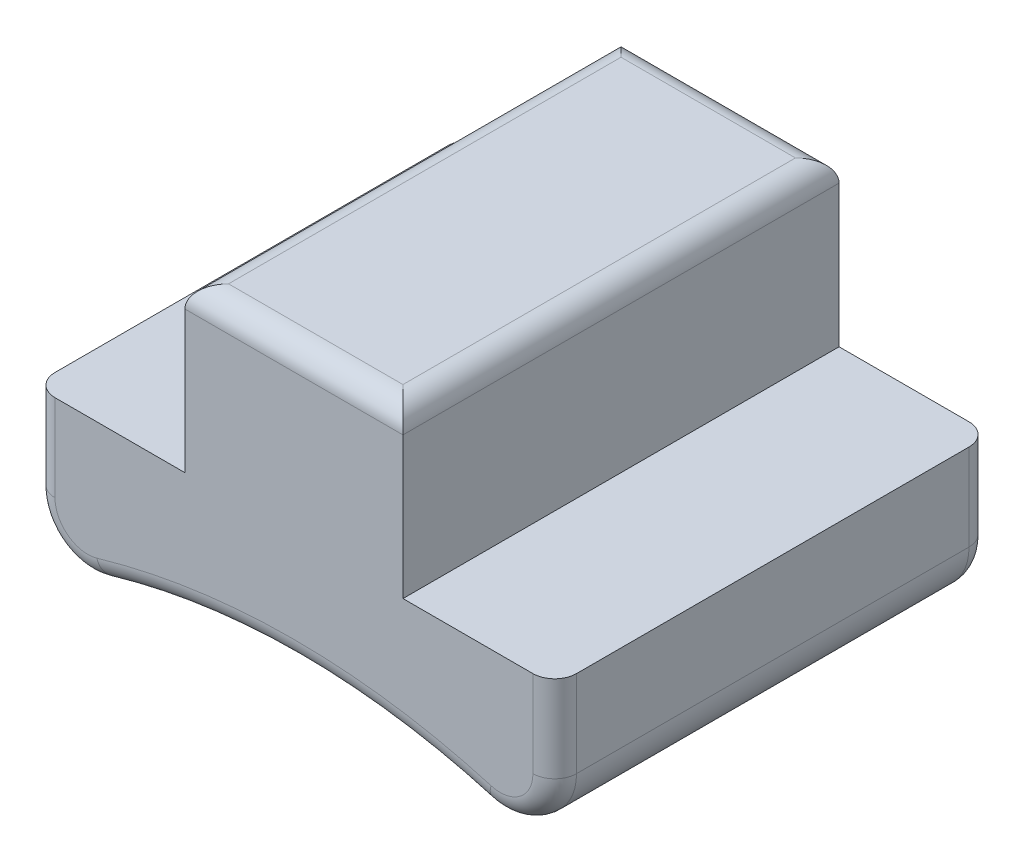
SolidWorks part; units mm, degrees
ref_plane "Front Plane" through (0, 0, 0) normal (0, 0, 1) x (1, 0, 0)
ref_plane "Top Plane" through (0, 0, 0) normal (0, 1, 0) x (1, 0, 0)
ref_plane "Right Plane" through (0, 0, 0) normal (1, 0, 0) x (0, 0, -1)
sketch "Sketch1" plane through (0, 0, 0) normal (0, 0, 1) x (1, 0, 0)
  line L0 (0, 0) -> (0, 120.9016) construction
  line L1 (-12.7, 111.4329) -> (12.7, 111.4329)
  line L2 (12.7, 111.4329) -> (12.7, 92.3829)
  line L3 (12.7, 92.3829) -> (30.3755, 92.3829)
  line L4 (30.3755, 92.3829) -> (30.3755, 73.3329)
  line L5 (-12.7, 111.4329) -> (-12.7, 92.3829)
  line L6 (-12.7, 92.3829) -> (-30.3755, 92.3829)
  line L7 (-30.3755, 92.3829) -> (-30.3755, 73.3329)
  line L8 (-30.3755, 73.3329) -> (0, 0) construction
  line L9 (0, 0) -> (30.3755, 73.3329) construction
  arc A0 (30.3755, 73.3329) -> (-30.3755, 73.3329) centre (0, 0) ccw
  point P10 (0, 111.4329)
  dimension "D1" = 158.75
  dimension "D2" = 45
  dimension "D3" = 25.4
  dimension "D4" = 19.05
  dimension "D5" = 19.05
extrude "Boss-Extrude1" add sketch "Sketch1" along normal blind 50.8
fillet "Fillet1" radius 6.35 2 edges at (-30.3755, 73.3329, 25.4) (30.3755, 73.3329, 25.4)
fillet "Fillet3" radius 2.54 4 edges at (12.7, 111.4329, 25.4) (0, 111.4329, 50.8) (-12.7, 111.4329, 25.4) (0, 111.4329, 0)
fillet "Fillet4" radius 2.54 5 edges at (-30.3755, 87.3362, 50.8) (-27.8348, 77.2089, 50.8) (30.3755, 87.3362, 50.8) (27.8348, 77.2089, 50.8) (0, 79.375, 50.8)
fillet "Fillet5" radius 2.54 5 edges at (-30.3755, 87.3362, 0) (-27.8348, 77.2089, 0) (30.3755, 87.3362, 0) (27.8348, 77.2089, 0) (0, 79.375, 0)
